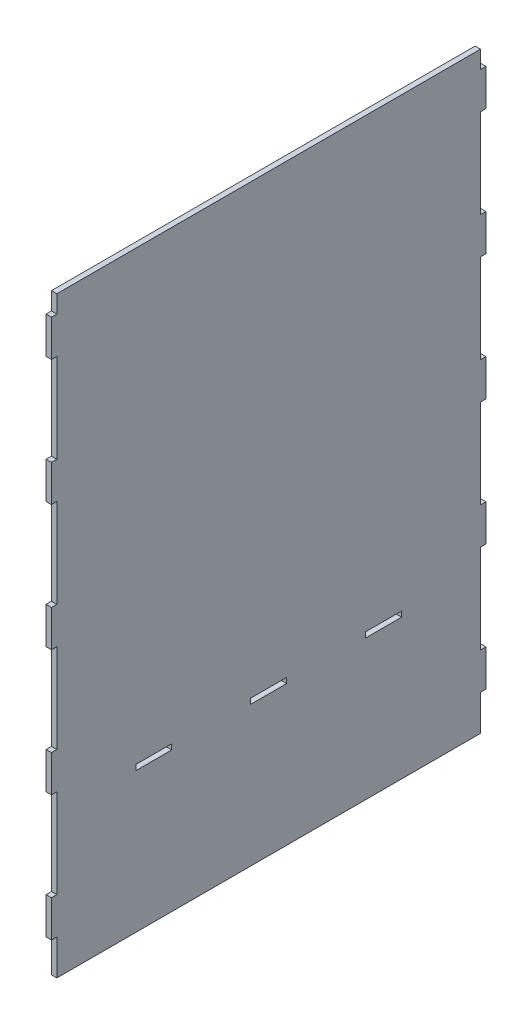
SolidWorks part; units mm, degrees
ref_plane "Спереди" through (0, 0, 0) normal (0, 0, 1) x (1, 0, 0)
ref_plane "Сверху" through (0, 0, 0) normal (0, 1, 0) x (1, 0, 0)
ref_plane "Справа" through (0, 0, 0) normal (1, 0, 0) x (0, 0, -1)
sketch "Эскиз1" plane through (0, 0, 0) normal (1, 0, 0) x (0, 0, -1)
  line L0 (-118, -165) -> (-118, -145.2)
  line L1 (-118, -165) -> (118, -165)
  line L2 (-118, -165) -> (-118, -145.2)
  line L3 (-118, 165) -> (118, 165)
  line L4 (118, -165) -> (118, -145.2)
  line L5 (-118, -165) -> (118, 165) construction
  line L6 (-118, 165) -> (118, -165) construction
  line L7 (-118, -145.2) -> (-121, -145.2)
  line L8 (-121, -145.2) -> (-121, -124.8)
  line L9 (-121, -124.8) -> (-118, -124.8)
  line L10 (0, -165) -> (0, 280.3639) construction
  line L11 (117.5, 0) -> (-358.1764, 0) construction
  line L12 (-118, -165) -> (-118, -145.2)
  line L13 (118, -124.8) -> (118, -75.2)
  line L14 (118, -105) -> (118, -87)
  line L15 (-118, -124.8) -> (-118, -75.2)
  line L16 (118, 134.8) -> (121, 134.8)
  line L17 (121, 155.2) -> (118, 155.2)
  line L18 (121, 134.8) -> (121, 155.2)
  line L19 (-118, -75.2) -> (-121, -75.2)
  line L20 (-121, -75.2) -> (-121, -54.8)
  line L21 (-121, -54.8) -> (-118, -54.8)
  line L22 (-118, -5.2) -> (-121, -5.2)
  line L23 (-121, -5.2) -> (-121, 15.2)
  line L24 (-121, 15.2) -> (-118, 15.2)
  line L25 (-118, 64.8) -> (-121, 64.8)
  line L26 (-121, 64.8) -> (-121, 85.2)
  line L27 (-121, 85.2) -> (-118, 85.2)
  line L28 (-118, 134.8) -> (-121, 134.8)
  line L29 (-121, 134.8) -> (-121, 155.2)
  line L30 (-121, 155.2) -> (-118, 155.2)
  line L31 (121, 85.2) -> (118, 85.2)
  line L32 (121, 64.8) -> (121, 85.2)
  line L33 (118, 64.8) -> (121, 64.8)
  line L34 (121, 15.2) -> (118, 15.2)
  line L35 (121, -5.2) -> (121, 15.2)
  line L36 (118, -5.2) -> (121, -5.2)
  line L37 (118, -75.2) -> (121, -75.2)
  line L38 (121, -75.2) -> (121, -54.8)
  line L39 (121, -54.8) -> (118, -54.8)
  line L40 (121, -124.8) -> (118, -124.8)
  line L41 (118, -145.2) -> (121, -145.2)
  line L42 (121, -145.2) -> (121, -124.8)
  line L43 (-118, 155.2) -> (-118, 165)
  line L44 (118, 155.2) -> (118, 165)
  line L45 (118, 85.2) -> (118, 134.8)
  line L46 (-118, 85.2) -> (-118, 134.8)
  line L47 (118, 15.2) -> (118, 64.8)
  line L48 (-118, 15.2) -> (-118, 64.8)
  line L49 (-118, -54.8) -> (-118, -5.2)
  line L50 (118, -54.8) -> (118, -5.2)
  line L51 (-118, -124.8) -> (-118, -105)
  line L52 (-118, -165) -> (-118, -145.2)
  line L53 (-74, -87) -> (-54, -87)
  line L54 (-10, -87) -> (10, -87)
  line L55 (-74, -87) -> (-74, -84)
  line L56 (-74, -84) -> (-54, -84)
  line L57 (-54, -87) -> (-54, -84)
  line L58 (-10, -84) -> (10, -84)
  line L59 (-10, -87) -> (-10, -84)
  line L60 (10, -87) -> (10, -84)
  line L61 (54, -84) -> (74, -84)
  line L62 (54, -87) -> (54, -84)
  line L63 (74, -87) -> (74, -84)
  line L64 (54, -87) -> (74, -87)
  line L66 (-118, -124.8) -> (-118, -87)
  point P0 (0, 0)
  point P56 (119, -5.2)
  dimension "D3" = 18
  dimension "D9" = 3
  dimension "D1" = 330
  dimension "D2" = 236
  dimension "D4" = 60
  dimension "D5" = 20.4
  dimension "D6" = 3
  dimension "D7" = 19.8
  dimension "D10" = 44
  dimension "D11" = 20
  dimension "D8" = 5
extrude "Бобышка-Вытянуть1" add sketch "Эскиз1" along normal blind 3 contours L39 L50 L36 L35 L34 L47 L33 L32 L31 L45 L16 L18 L17 L44 L3 L43 L30 L29 L28 L46 L27 L26 L25 L48 L24 L23 L22 L49 L21 L20 L19 L15 L9 L8 L7 L0 L1 L4 L41 L42 L40 L13 L37 L38 L64 L62
